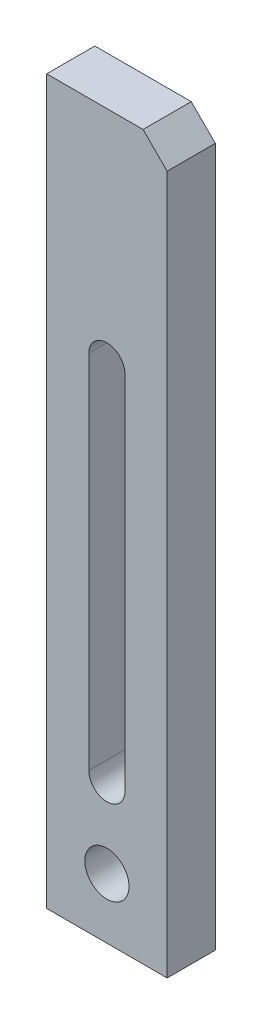
SolidWorks part; units mm, degrees
ref_plane "前视基准面" through (0, 0, 0) normal (0, 0, 1) x (1, 0, 0)
ref_plane "上视基准面" through (0, 0, 0) normal (0, 1, 0) x (1, 0, 0)
ref_plane "右视基准面" through (0, 0, 0) normal (1, 0, 0) x (0, 0, -1)
sketch "草图1" plane through (0, 0, 0) normal (0, 0, 1) x (1, 0, 0)
  line L1 (-15, 90) -> (15, 90)
  line L2 (-15, 90) -> (-15, -90)
  line L3 (-15, -90) -> (15, -90)
  line L4 (15, 90) -> (15, -90)
  line L5 (-15, 90) -> (15, -90) construction
  line L6 (-15, -90) -> (15, 90) construction
  point P0 (0, 0)
  dimension "D1" = 30
  dimension "D2" = 180
extrude "凸台-拉伸1" add sketch "草图1" along normal blind 12
sketch "草图2" plane through (0, 0, 12) normal (0, 0, 1) x (1, 0, 0)
  line L0 (0, 35) -> (0, -55) construction
  line L1 (4.5, 35) -> (4.5, -55)
  line L2 (-4.5, 35) -> (-4.5, -55)
  line L3 (-15, -90) -> (15, -90) construction
  line L4 (-15, 90) -> (-15, -90) construction
  arc A0 (4.5, 35) -> (-4.5, 35) centre (0, 35) ccw
  arc A1 (-4.5, -55) -> (4.5, -55) centre (0, -55) ccw
  circle A2 centre (0, -75) radius 5.5
  point P3 (0, -10)
  dimension "D4" = 11
  dimension "D1" = 9
  dimension "D2" = 90
  dimension "D3" = 20
  dimension "D5" = 15
  dimension "D6" = 15
extrude "切除-拉伸1" cut sketch "草图2" against normal blind 12
chamfer "倒角1" distance 6 angle 45 1 edges at (15, 90, 6)
